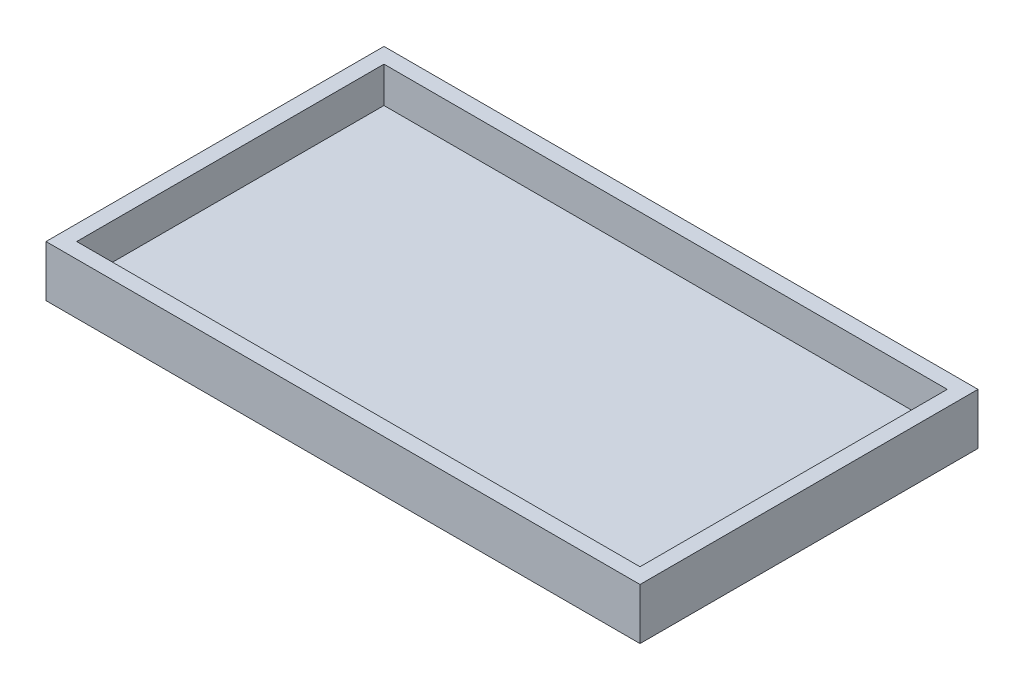
SolidWorks part; units mm, degrees
material "ABS"
ref_plane "Front Plane" through (0, 0, 0) normal (0, 0, 1) x (1, 0, 0)
ref_plane "Top Plane" through (0, 0, 0) normal (0, 1, 0) x (1, 0, 0)
ref_plane "Right Plane" through (0, 0, 0) normal (1, 0, 0) x (0, 0, -1)
sketch "Sketch1" plane through (0, 0, 0) normal (0, 1, 0) x (1, 0, 0)
  line L1 (0, 0) -> (116, 0)
  line L2 (0, 0) -> (0, 66)
  line L3 (0, 66) -> (116, 66)
  line L4 (116, 0) -> (116, 66)
  dimension "D1" = 116
  dimension "D2" = 66
extrude "Boss-Extrude1" add sketch "Sketch1" along normal blind 10
shell "Shell1" thickness 3
